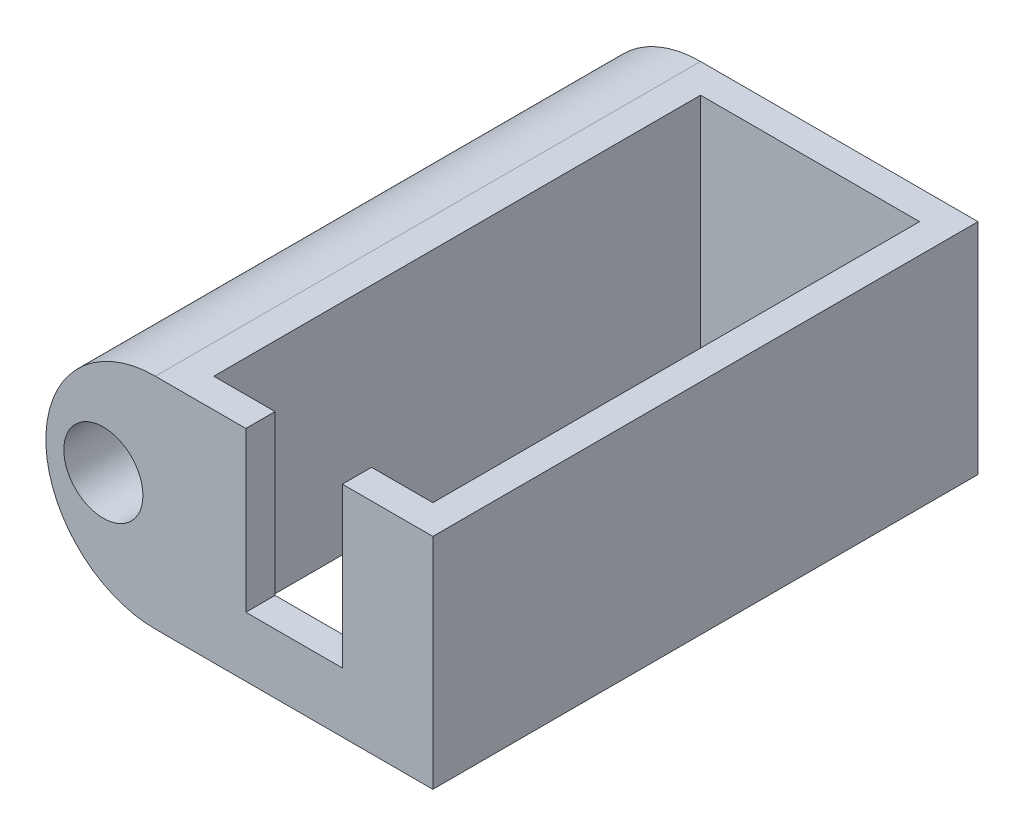
SolidWorks part; units mm, degrees
ref_plane "Front Plane" through (0, 0, 0) normal (0, 0, 1) x (1, 0, 0)
ref_plane "Top Plane" through (0, 0, 0) normal (0, 1, 0) x (1, 0, 0)
ref_plane "Right Plane" through (0, 0, 0) normal (1, 0, 0) x (0, 0, -1)
sketch "Sketch1" plane through (0, 0, 0) normal (0, 1, 0) x (1, 0, 0)
  line L0 (-1.2, -1.2) -> (-1.2, 21.2)
  line L1 (0, 0) -> (9, 0)
  line L2 (0, 0) -> (0, 20)
  line L3 (0, 20) -> (9, 20)
  line L4 (9, 0) -> (9, 20)
  line L5 (0, 0) -> (9, 20) construction
  line L6 (0, 20) -> (9, 0) construction
  line L7 (-1.2, 21.2) -> (10.2, 21.2)
  line L8 (10.2, -1.2) -> (10.2, 21.2)
  line L9 (-1.2, -1.2) -> (10.2, -1.2)
  point P4 (4.5, 10)
  dimension "D1" = 20
  dimension "D2" = 9
  dimension "D3" = 1.2
extrude "Boss-Extrude1" add sketch "Sketch1" along normal blind 9 contours L0 L9 L8 L7 L4 L1 L2 L3
sketch "Sketch2" plane through (0, 0, 1.2) normal (0, 0, 1) x (1, 0, 0)
  line L0 (2.5171, 9) -> (6.4829, 9)
  line L2 (-1.2, 9) -> (10.2, 9) construction
  line L8 (2.5171, 9) -> (6.4829, 9)
  line L9 (2.5171, 9) -> (2.5171, 2.4593)
  line L10 (2.5171, 2.4593) -> (6.4829, 2.4593)
  line L11 (6.4829, 9) -> (6.4829, 2.4593)
  line L12 (2.5171, 9) -> (6.4829, 2.4593) construction
  line L13 (2.5171, 2.4593) -> (6.4829, 9) construction
  point P5 (4.5, 9)
  point P7 (4.5, 5.7297)
  line M3 (10.2, 9) -> (-1.2, 9)
extrude "Cut-Extrude1" cut sketch "Sketch2" against normal up to next contours L11 L9 L10 M3
sketch "Sketch3" plane through (0, 0, 1.2) normal (0, 0, 1) x (1, 0, 0)
  line L0 (-1.2, 9) -> (-1.2, 0) construction
  line L1 (-1.2, 9) -> (-1.2, 0)
  circle A0 centre (-3.3376, 4.5) radius 1.625
  arc A1 (-1.2, 9) -> (-1.2, 0) centre (-1.2, 4.5) ccw
  point P5 (-1.2, 4.5)
  dimension "D1" = 3.25
extrude "Boss-Extrude2" add sketch "Sketch3" against normal up to surface (22.4 mm away) up to face at (4.5, 4.5, -21.2)
sketch "Sketch4" plane through (0, 0, 0) normal (1, 0, 0) x (0, 0, -1)
  circle A0 centre (9.8992, 4.5) radius 1
extrude "Cut-Extrude2" cut sketch "Sketch4" against normal blind 10 from offset 4 offset against normal yes
sketch "Sketch5" plane through (0, 0, -21.2) normal (0, 0, -1) x (-1, 0, 0)
  circle A0 centre (3.3376, 4.5) radius 1.55
  circle A1 centre (3.3376, 4.5) radius 1.0019
  circle M7 centre (3.3376, 4.5) radius 1.625
extrude "Boss-Extrude3" add sketch "Sketch5" against normal blind 1 contours A1 M7
